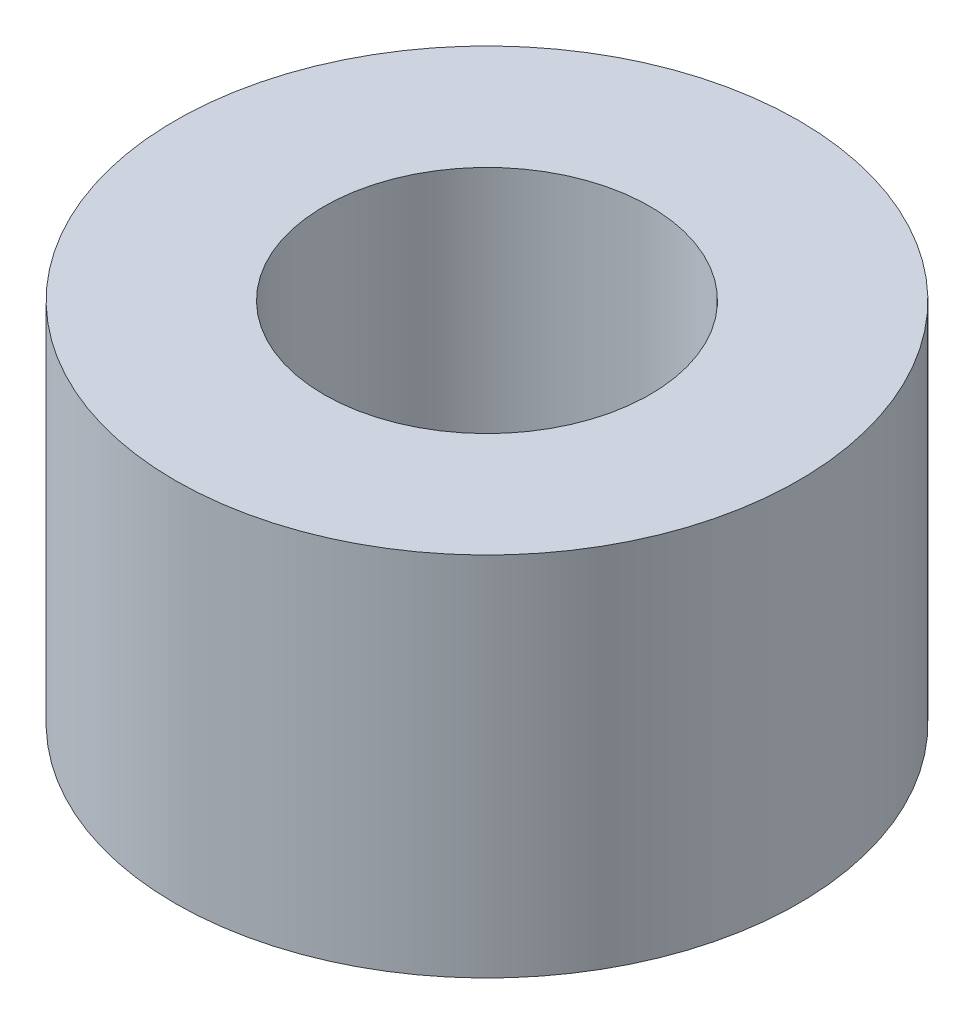
SolidWorks part; units mm, degrees
material "1.0035 (S185)"
ref_plane "Płaszczyzna przednia" through (0, 0, 0) normal (0, 0, 1) x (1, 0, 0)
ref_plane "Płaszczyzna górna" through (0, 0, 0) normal (0, 1, 0) x (1, 0, 0)
ref_plane "Płaszczyzna prawa" through (0, 0, 0) normal (1, 0, 0) x (0, 0, -1)
sketch "Szkic1" plane through (0, 0, 0) normal (0, 1, 0) x (1, 0, 0)
  circle A0 centre (0, 0) radius 4.255
  circle A1 centre (0, 0) radius 2.225
  dimension "D1" = 8.51
  dimension "D2" = 4.45
extrude "Dodanie-wyciągnięcie1" add sketch "Szkic1" along normal blind 5
